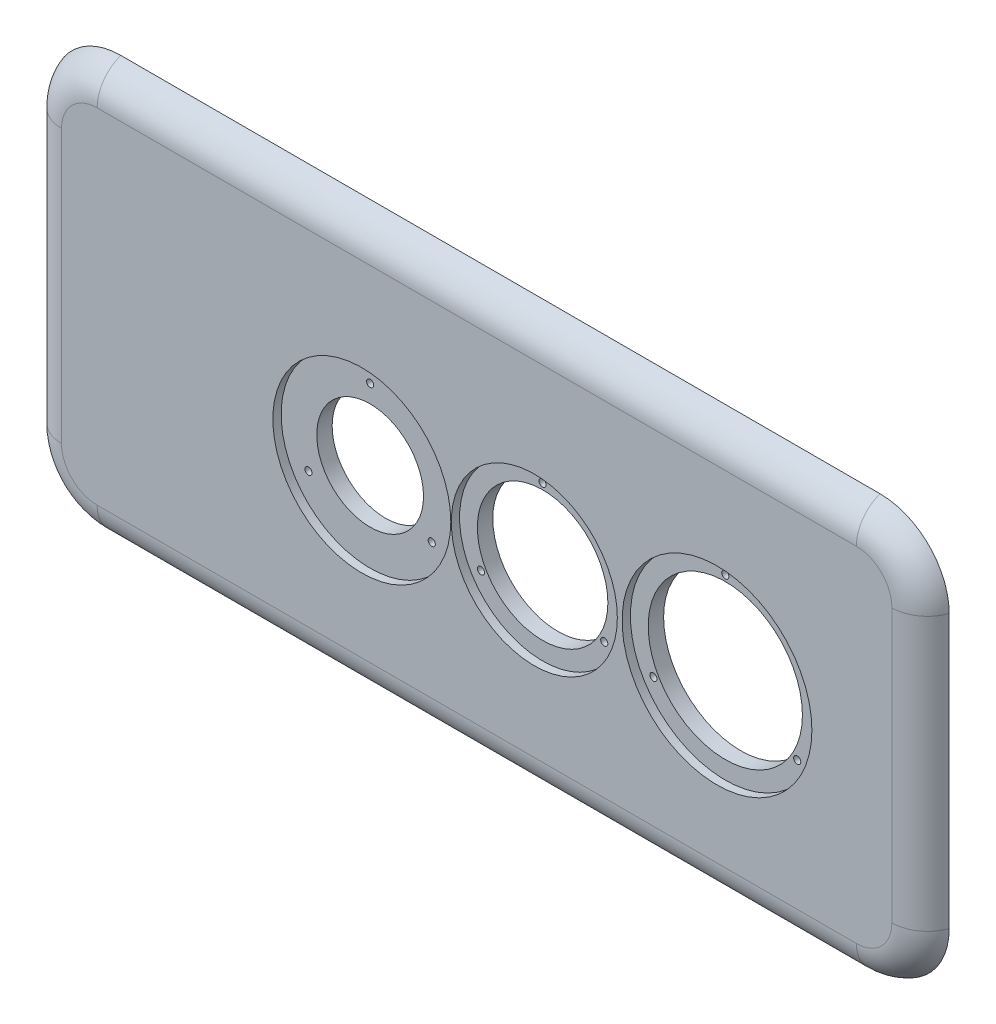
SolidWorks part; units mm, degrees
ref_plane "Front Plane" through (0, 0, 0) normal (0, 0, 1) x (1, 0, 0)
ref_plane "Top Plane" through (0, 0, 0) normal (0, 1, 0) x (1, 0, 0)
ref_plane "Right Plane" through (0, 0, 0) normal (1, 0, 0) x (0, 0, -1)
sketch "Sketch1" plane through (0, 0, 0) normal (0, 0, 1) x (1, 0, 0)
  line L1 (-337.1569, 207.6961) -> (422.8431, 207.6961)
  line L2 (-337.1569, 207.6961) -> (-337.1569, -142.3039)
  line L3 (-337.1569, -142.3039) -> (422.8431, -142.3039)
  line L4 (422.8431, 207.6961) -> (422.8431, -142.3039)
  dimension "D1" = 760
  dimension "D2" = 350
extrude "Boss-Extrude1" add sketch "Sketch1" along normal blind 38
sketch "Sketch2" plane through (0, 0, 38) normal (0, 0, 1) x (1, 0, 0)
  line L0 (422.8431, 207.6961) -> (422.8431, 24.6561)
  line L1 (422.8431, -142.3039) -> (422.8431, 207.6961) construction
  line L2 (422.8431, 24.6561) -> (245.4031, 24.6561)
  line L3 (245.4031, 24.6561) -> (91.4031, 24.6561)
  line L4 (91.4031, 24.6561) -> (-54.0069, 24.6561)
  circle A0 centre (245.4031, 24.6561) radius 65
  circle A1 centre (91.4031, 24.6561) radius 55
  circle A2 centre (-54.0069, 24.6561) radius 45
  dimension "D1" = 183.04
  dimension "D2" = 177.44
  dimension "D3" = 154
  dimension "D4" = 145.41
extrude "Cut-Extrude1" cut sketch "Sketch2" against normal through all
sketch "Sketch4" plane through (0, 0, 38) normal (0, 0, 1) x (1, 0, 0)
  circle A0 centre (-54.0069, 24.6561) radius 75
sketch "Sketch5" plane through (0, 0, 38) normal (0, 0, 1) x (1, 0, 0)
  circle A0 centre (91.4031, 24.6561) radius 70
extrude "Cut-Extrude2" cut sketch "Sketch4" against normal blind 7
extrude "Cut-Extrude3" cut sketch "Sketch5" against normal blind 7
sketch "Sketch12" plane through (0, 0, 38) normal (0, 0, 1) x (1, 0, 0)
  circle A0 centre (-54.0069, 24.6561) radius 60
  circle A1 centre (91.4031, 24.6561) radius 60
  circle A3 centre (-54.0069, 84.6561) radius 3
  circle A4 centre (-2.0453, -5.3439) radius 3
  circle A5 centre (-105.9684, -5.3439) radius 3
  circle A6 centre (91.4031, 84.6561) radius 3
  circle A7 centre (143.3647, -5.3439) radius 3
  circle A8 centre (39.4416, -5.3439) radius 3
  point P15 (-54.0069, 24.6561)
  point P22 (91.4031, 24.6561)
  dimension "D1" = 3
  dimension "D2" = 6
  dimension "D3" = 3
extrude "Cut-Extrude6" cut sketch "Sketch12" against normal through all contours A3 | A5 | A4 | A6 | A8 | A7
sketch "Sketch15" plane through (0, 0, 38) normal (0, 0, 1) x (1, 0, 0)
  line L1 (-277.1569, 207.6961) -> (362.8431, 207.6961)
  line L2 (-337.1569, 147.6961) -> (-337.1569, -82.3039)
  line L3 (-277.1569, -142.3039) -> (362.8431, -142.3039)
  line L4 (422.8431, 147.6961) -> (422.8431, -82.3039)
  arc A0 (362.8431, -142.3039) -> (422.8431, -82.3039) centre (362.8431, -82.3039) ccw
  arc A1 (422.8431, 147.6961) -> (362.8431, 207.6961) centre (362.8431, 147.6961) ccw
  arc A2 (-277.1569, -142.3039) -> (-337.1569, -82.3039) centre (-277.1569, -82.3039) cw
  arc A3 (-337.1569, 147.6961) -> (-277.1569, 207.6961) centre (-277.1569, 147.6961) cw
  point P8 (422.8431, -142.3039)
  point P15 (-337.1569, 207.6961)
  dimension "D1" = 60
extrude "Cut-Extrude7" cut sketch "Sketch15" against normal through all flip side to cut
fillet "Fillet1" radius 30 8 edges at (405.2695, 190.1225, 38) (422.8431, 32.6961, 38) (405.2695, -124.7303, 38) (42.8431, -142.3039, 38) (-319.5833, -124.7303, 38) (-337.1569, 32.6961, 38) (-319.5833, 190.1225, 38) (42.8431, 207.6961, 38)
sketch "Sketch16" plane through (0, 0, 0) normal (0, 0, -1) x (-1, 0, 0)
  line L1 (-422.8431, 207.6961) -> (337.1569, 207.6961)
  line L2 (-422.8431, 207.6961) -> (-422.8431, -142.3039)
  line L3 (-422.8431, -142.3039) -> (337.1569, -142.3039)
  line L4 (337.1569, 207.6961) -> (337.1569, -142.3039)
extrude "Cut-Extrude8" cut sketch "Sketch16" against normal blind 18
sketch "Sketch17" plane through (0, 0, 38) normal (0, 0, 1) x (1, 0, 0)
  circle A0 centre (245.4031, 24.6561) radius 80
  circle A1 centre (245.4031, 24.6561) radius 70
  circle A2 centre (245.4031, 94.6561) radius 3
  circle A3 centre (306.0249, -10.3439) radius 3
  circle A4 centre (184.7814, -10.3439) radius 3
  point P12 (245.4031, 24.6561)
  circle M13 centre (245.4031, 24.6561) radius 65
  dimension "D1" = 3
extrude "Cut-Extrude9" cut sketch "Sketch17" against normal blind 7 contours A0 A4 A1 A2 A3 | A4 A1 A3 A2 M13
sketch "Sketch18" plane through (0, 0, 38) normal (0, 0, 1) x (1, 0, 0)
  circle A0 centre (245.4031, 94.6561) radius 3
  circle A1 centre (184.7814, -10.3439) radius 3
  circle A2 centre (306.0249, -10.3439) radius 3
extrude "Cut-Extrude10" cut sketch "Sketch18" against normal up to surface (20 mm away) up to face at (42.8431, 32.6961, 18)
